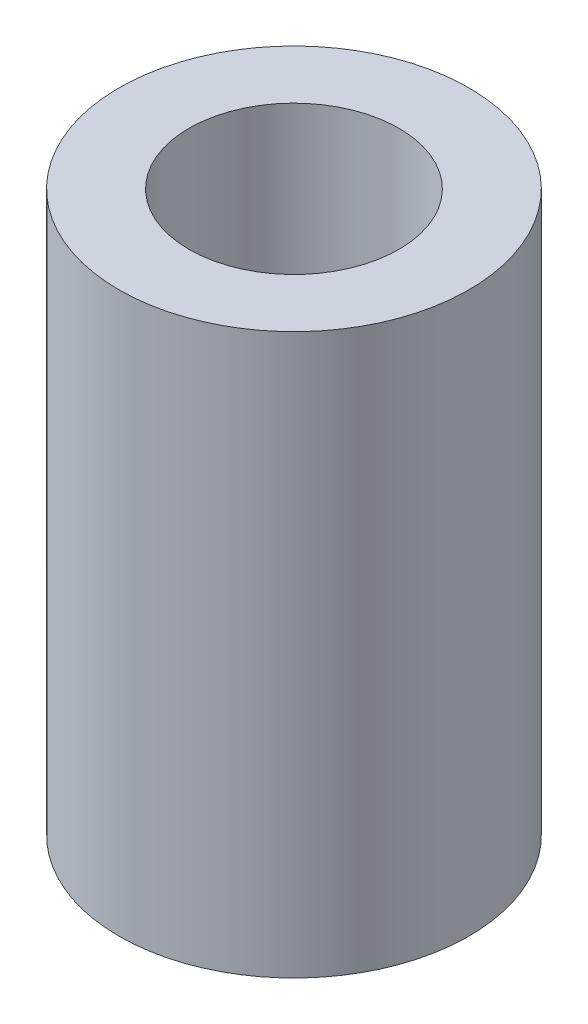
SolidWorks part; units mm, degrees
ref_plane "Front Plane" through (0, 0, 0) normal (0, 0, 1) x (1, 0, 0)
ref_plane "Top Plane" through (0, 0, 0) normal (0, 1, 0) x (1, 0, 0)
ref_plane "Right Plane" through (0, 0, 0) normal (1, 0, 0) x (0, 0, -1)
sketch "Sketch1" plane through (0, 0, 0) normal (0, 1, 0) x (1, 0, 0)
  circle A0 centre (-0.4889, 0.1146) radius 2.5
  circle A1 centre (-0.4889, 0.1146) radius 1.5
  dimension "D1" = 5
extrude "Boss-Extrude1" add sketch "Sketch1" against normal blind 8
